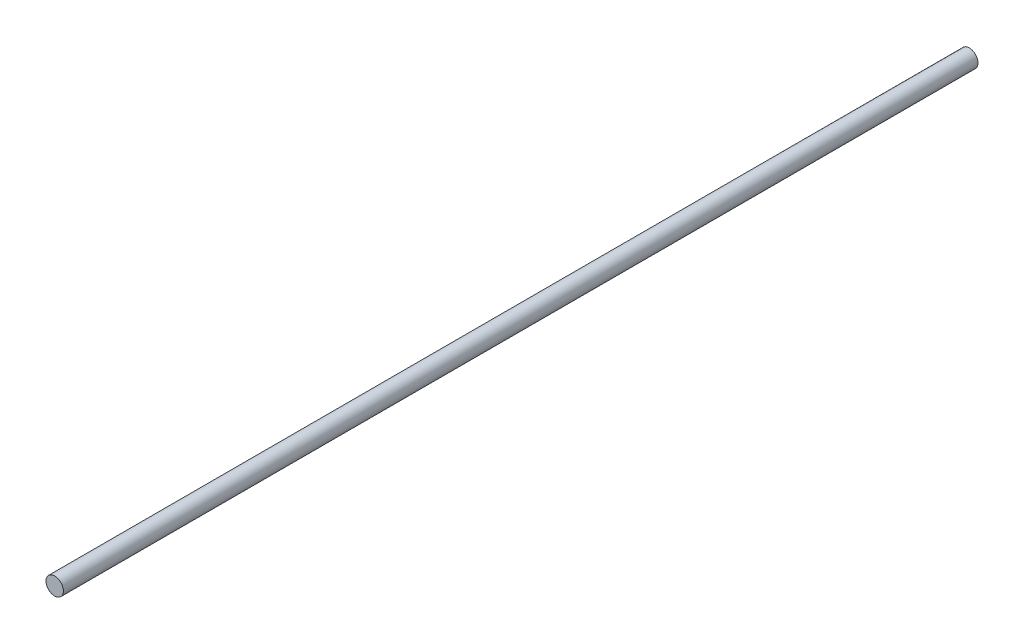
SolidWorks part; units mm, degrees
ref_plane "Front Plane" through (0, 0, 0) normal (0, 0, 1) x (1, 0, 0)
ref_plane "Top Plane" through (0, 0, 0) normal (0, 1, 0) x (1, 0, 0)
ref_plane "Right Plane" through (0, 0, 0) normal (1, 0, 0) x (0, 0, -1)
sketch "Sketch1" plane through (0, 0, 0) normal (0, 0, 1) x (1, 0, 0)
  circle A0 centre (0, 0) radius 4.7625
  dimension "D1" = 9.525
extrude "Boss-Extrude1" add sketch "Sketch1" along normal blind 500
